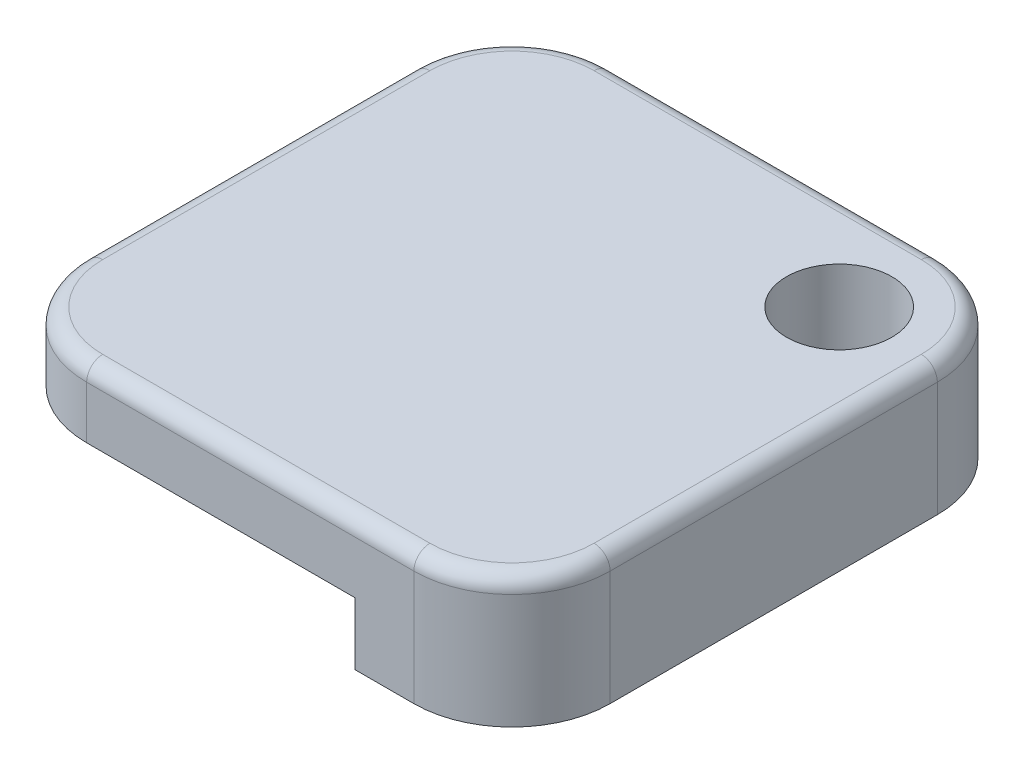
SolidWorks part; units mm, degrees
ref_plane "Front Plane" through (0, 0, 0) normal (0, 0, 1) x (1, 0, 0)
ref_plane "Top Plane" through (0, 0, 0) normal (0, 1, 0) x (1, 0, 0)
ref_plane "Right Plane" through (0, 0, 0) normal (1, 0, 0) x (0, 0, -1)
sketch "Sketch1" plane through (0, 0, 0) normal (0, 1, 0) x (1, 0, 0)
  line L1 (-12.7, 12.7) -> (12.7, 12.7)
  line L2 (-12.7, 12.7) -> (-12.7, -12.7)
  line L3 (-12.7, -12.7) -> (12.7, -12.7)
  line L4 (12.7, 12.7) -> (12.7, -12.7)
  line L5 (-12.7, 12.7) -> (12.7, -12.7) construction
  line L6 (-12.7, -12.7) -> (12.7, 12.7) construction
  point P0 (0, 0)
  dimension "D1" = 25.4
extrude "Boss-Extrude1" add sketch "Sketch1" along normal blind 6.35
sketch "Sketch2" plane through (0, 0, 0) normal (0, -1, 0) x (1, 0, 0)
  line L0 (12.7, 12.7) -> (12.7, -12.7) construction
  line L1 (-12.7, 12.7) -> (5.08, 12.7)
  line L2 (-12.7, 12.7) -> (-12.7, -5.08)
  line L3 (-12.7, -5.08) -> (5.08, -5.08)
  line L4 (5.08, 12.7) -> (5.08, -5.08)
  dimension "D1" = 7.62
extrude "Cut-Extrude1" cut sketch "Sketch2" against normal blind 3.0226
fillet "Fillet1" radius 4.7625 4 edges at (-12.7, 4.6863, 12.7) (-12.7, 3.175, -12.7) (12.7, 3.175, -12.7) (12.7, 3.175, 12.7)
hole_wizard "#10 Clearance Hole1" positions "Sketch3" profile "Sketch4" hole size "#10" standard "ANSI Inch"
sketch "Sketch3" plane through (0, 6.35, 0) normal (0, 1, 0) x (1, 0, 0)
  point P8 (7.9375, 7.9375)
  point P14 (0, 0)
  point P15 (7.9375, 7.9375)
sketch "Sketch4" plane through (7.9375, 6.35, -7.9375) normal (1, 0, 0) x (0, 0, 1)
  line L0 (0, 0) -> (0, 12.2018)
  line L1 (0, 12.2018) -> (2.5527, 10.668)
  line L2 (2.5527, 10.668) -> (2.5527, 0)
  line L5 (2.5527, 0) -> (0, 0)
  line L10 (0, 12.2018) -> (-2.5527, 10.668) construction
  line L11 (0, -6.35) -> (0, 107.95) construction
  dimension "Hole Dia." = 5.1054
  dimension "Hole Depth" = 10.668
  dimension "Drill Angle" = 118
fillet "Fillet2" radius 0.78 8 edges at (11.3051, 6.35, -11.3051) (12.7, 6.35, 0) (11.3051, 6.35, 11.3051) (0, 6.35, 12.7) (-11.3051, 6.35, 11.3051) (-12.7, 6.35, 0) (-11.3051, 6.35, -11.3051) (0, 6.35, -12.7)
